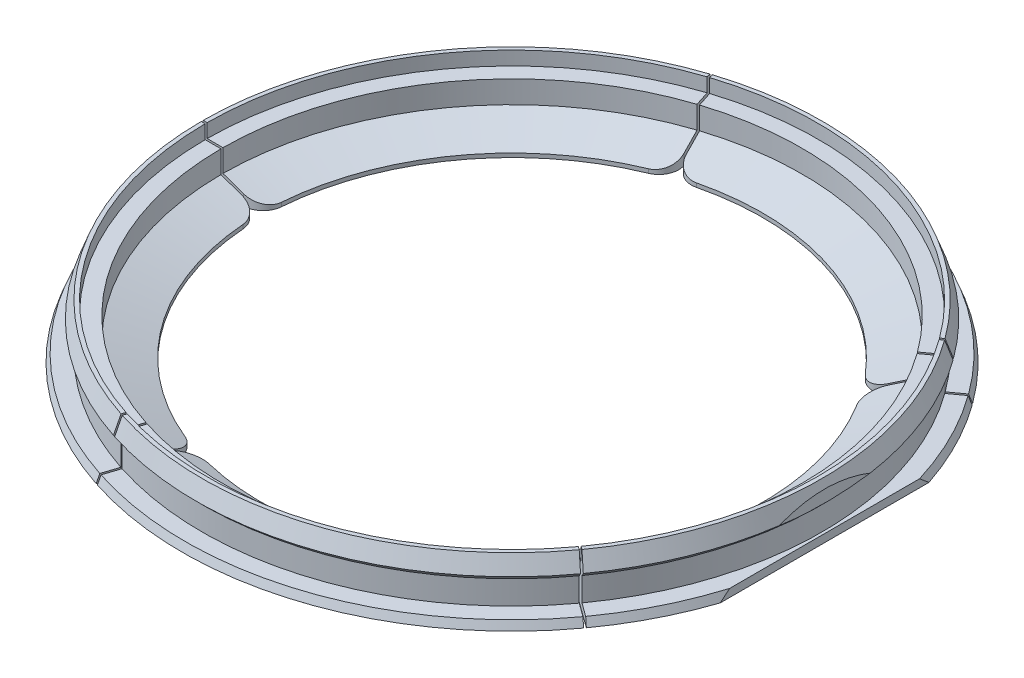
SolidWorks part; units mm, degrees
ref_plane "Front Plane" through (0, 0, 0) normal (0, 0, 1) x (1, 0, 0)
ref_plane "Top Plane" through (0, 0, 0) normal (0, 1, 0) x (1, 0, 0)
ref_plane "Right Plane" through (0, 0, 0) normal (1, 0, 0) x (0, 0, -1)
sketch "Sketch1" plane through (0, 0, 0) normal (0, 0, 1) x (1, 0, 0)
  line L0 (63.5, 0) -> (63.5, 1)
  line L1 (63.5, 1) -> (73.5, 4.5348)
  line L3 (77.5, 13.7) -> (78.5, 13.7)
  line L4 (78.5, 13.7) -> (80.0328, 9.5)
  line L5 (83.5, 0) -> (63.5, 0)
  line L6 (0, 0) -> (0, 20.8567) construction
  line L7 (77.5, 10.2) -> (73.5, 10.2)
  line L8 (73.5, 10.2) -> (73.5, 4.5348)
  line L10 (77.5, 10.2) -> (77.5, 13.7)
  line L11 (80.0328, 9.5) -> (78.5328, 8)
  line L12 (78.5328, 8) -> (78.5328, 2)
  line L13 (78.5328, 2) -> (82.7701, 2)
  line L14 (82.7701, 2) -> (83.5, 0)
  point P12 (0, 0)
  point P17 (0, 0)
  point P18 (0, 0)
  point P19 (79.1184, 2.2496)
  point P20 (0, 0)
  dimension "D1" = 13.7
  dimension "D2" = 1
  dimension "D3" = 6
  dimension "D4" = 10
  dimension "D5" = 10
  dimension "D6" = 1
  dimension "D7" = 77.5
  dimension "D8" = 45
  dimension "D9" = 2
  dimension "D10" = 4
  dimension "D11" = 3.5
  dimension "D12" = 6
  dimension "D13" = 1.5
revolve "Revolve1" add sketch "Sketch1" angle 360 about L6
sketch "Sketch2" plane through (0, 0, 0) normal (0, 1, 0) x (1, 0, 0)
  line L0 (79.2, 26.4501) -> (79.2, -26.4501)
  circle A0 centre (0, 0) radius 83.5 construction
  arc A1 (79.2, -26.4501) -> (79.2, 26.4501) centre (0, 0) ccw
  dimension "D1" = 4.3
extrude "Cut-Extrude1" cut sketch "Sketch2" along normal through all
sketch "Sketch4" plane through (0, 0, 0) normal (0, 1, 0) x (1, 0, 0)
  line L0 (-31.1025, 96.5325) -> (-31.578, 96.378)
  line L5 (-101.4191, 0.25) -> (-49.0052, 0.25)
  line L6 (-101.4191, 0.25) -> (-101.4191, -0.25)
  line L7 (-101.4191, -0.25) -> (-49.0052, -0.25)
  line L8 (-49.0052, 0.25) -> (-49.0052, -0.25)
  line L13 (-31.1025, 96.5325) -> (-14.9057, 46.684)
  line L14 (-14.9057, 46.684) -> (-15.3812, 46.5295)
  line L20 (-31.578, 96.378) -> (-15.3812, 46.5295)
  line L24 (82.1967, 59.4104) -> (81.9028, 59.8149)
  line L25 (82.1967, 59.4104) -> (39.793, 28.6023)
  line L26 (39.793, 28.6023) -> (39.4991, 29.0068)
  line L31 (81.9028, 59.8149) -> (39.4991, 29.0068)
  line L32 (81.9028, -59.8149) -> (82.1967, -59.4104)
  line L33 (81.9028, -59.8149) -> (39.4991, -29.0068)
  line L34 (39.4991, -29.0068) -> (39.793, -28.6023)
  line L35 (82.1967, -59.4104) -> (39.793, -28.6023)
  line L36 (-31.578, -96.378) -> (-31.1025, -96.5325)
  line L37 (-31.578, -96.378) -> (-15.3812, -46.5295)
  line L38 (-15.3812, -46.5295) -> (-14.9057, -46.684)
  line L39 (-31.1025, -96.5325) -> (-14.9057, -46.684)
  point P4 (-49.0052, 0)
  point P25 (0, 0)
  dimension "D1" = 0.5
extrude "Cut-Extrude3" cut sketch "Sketch4" along normal through all both and the other way through all
sketch "Sketch5" plane through (0, 0, 0) normal (0, 1, 0) x (1, 0, 0)
  line L0 (-37.4017, -80.2082) -> (0, 0) construction
  line L1 (0, 0) -> (0, -18.0859) construction
  line L2 (0, 0) -> (22.9055, 85.4844) construction
  circle A0 centre (-37.4017, -80.2082) radius 2.15
  circle A1 centre (22.9055, 85.4844) radius 2.15
  arc A2 (-42.2035, -78.8143) -> (-33.2474, -82.9906) centre (-37.4017, -80.2082) ccw
  arc A4 (27.8764, 84.9455) -> (18.3311, 87.5032) centre (22.9055, 85.4844) ccw
  arc A5 (79.2, -26.4501) -> (79.2, 26.4501) centre (0, 0) ccw construction
  arc A7 (-42.2035, -78.8143) -> (-46.1758, -67.7628) centre (-51.807, -76.0265) ccw
  arc A8 (-33.2474, -82.9906) -> (-22.228, -78.9298) centre (-24.9388, -88.5554) cw
  arc A9 (27.8764, 84.9455) -> (33.7074, 74.7516) centre (37.8181, 83.8677) ccw
  arc A10 (18.3311, 87.5032) -> (8.1843, 81.5905) centre (9.1824, 91.5406) cw
  arc A11 (33.7074, 74.7516) -> (8.1843, 81.5905) centre (0, 0) ccw
  arc A12 (-46.1758, -67.7628) -> (-22.228, -78.9298) centre (0, 0) ccw
  dimension "D1" = 4.3
  dimension "D4" = 10
  dimension "D5" = 5
  dimension "D6" = 1.5
  dimension "D2" = 25
  dimension "D3" = 15
extrude "Boss-Extrude1" [suppressed] add sketch "Sketch5" along normal blind 4 separate body
sketch "Sketch6" plane through (0, 0, 0) normal (0, 1, 0) x (1, 0, 0)
  line L1 (-76.56, 24.8759) -> (0, 0) construction
  line L2 (0, 0) -> (0, -17.4609) construction
  line L3 (-83.4144, 3.7804) -> (-69.7057, 45.9713)
  line L4 (9.8105, -79.9) -> (0, 0) construction
  line L5 (31.8262, -77.1968) -> (-12.2053, -82.6032)
  arc A2 (-69.7057, 45.9713) -> (-83.4144, 3.7804) centre (0, 0) ccw
  arc A3 (79.2, -26.4501) -> (79.2, 26.4501) centre (0, 0) ccw construction
  arc A5 (-12.2053, -82.6032) -> (31.8262, -77.1968) centre (0, 0) ccw
  point P12 (9.8105, -79.9)
  dimension "D1" = 3
  dimension "D3" = 3
  dimension "D2" = 108
  dimension "D4" = 7
extrude "Cut-Extrude10" [suppressed] cut sketch "Sketch6" along normal blind 10 contours A2 L3 | L5 A5
fillet "Fillet2" radius 5 2 edges at (-19.8602, 0.5, -60.3144) (-63.4995, 0.5, -0.25)
fillet "Fillet3" radius 5 2 edges at (-19.8602, 0.5, 60.3144) (-63.4995, 0.5, 0.25)
fillet "Fillet4" radius 5 2 edges at (51.2252, 0.5, 37.5263) (-19.3847, 0.5, 60.4689)
fillet "Fillet5" radius 5 2 edges at (51.5191, 0.5, -37.1218) (51.5191, 0.5, 37.1218)
fillet "Fillet6" radius 5 2 edges at (51.2252, 0.5, -37.5263) (-19.3847, 0.5, -60.4689)
equation "\"gg\"=5"
